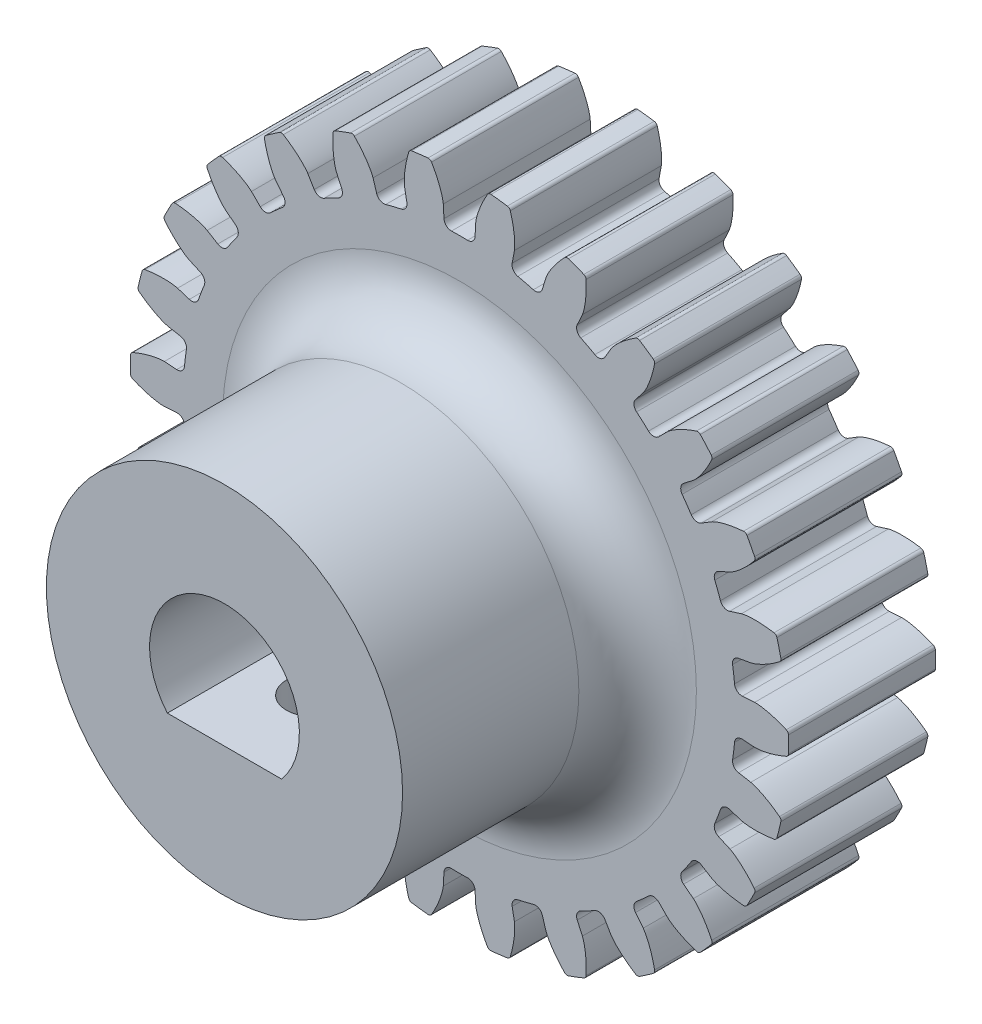
SolidWorks part; units mm, degrees
material "ABS"
ref_plane "Front" through (0, 0, 0) normal (0, 0, 1) x (1, 0, 0)
ref_plane "Top" through (0, 0, 0) normal (0, 1, 0) x (1, 0, 0)
ref_plane "Right" through (0, 0, 0) normal (1, 0, 0) x (0, 0, -1)
sketch "Sketch1" plane through (0, 0, 0) normal (0, 0, 1) x (1, 0, 0)
  circle A0 centre (0, 0) radius 14.224
extrude "Boss-Extrude1" add sketch "Sketch1" along normal blind 6.35
sketch "Sketch3" plane through (0, 0, 0) normal (0, 0, 1) x (1, 0, 0)
  line L0 (0, 0) -> (43.7181, 0) construction
  line L2 (0, 0) -> (-0.6547, 11.92) construction
  line L3 (0, 0) -> (0.6547, 11.92) construction
  line L4 (0.6547, 11.92) -> (0.7013, 12.768) construction
  line L5 (0, 0) -> (0, 61.276) construction
  line L6 (-0.6547, 11.92) -> (-0.7013, 12.768) construction
  circle A0 centre (0, 0) radius 14.224 construction
  circle A1 centre (0, 0) radius 13.208 construction
  circle A2 centre (0, 0) radius 12.7873 construction
  arc A3 (0.6547, 11.92) -> (-0.6547, 11.92) centre (0, 0) ccw construction
  arc A5 (1.2601, 14.1681) -> (-1.2601, 14.1681) centre (0, 0) ccw
  spline S0 degree 4 poles (-0.7013, 12.768) (-0.7014, 12.7703) (-0.7019, 12.7766) (-0.7031, 12.7884) (-0.7055, 12.8077) (-0.709, 12.8323) (-0.7143, 12.864) (-0.7215, 12.9013) (-0.7302, 12.9422) (-0.7407, 12.9866) (-0.752, 13.0308) (-0.7641, 13.0749) (-0.777, 13.1187) (-0.7933, 13.1717) (-0.8142, 13.2351) (-0.8403, 13.3091) (-0.872, 13.3928) (-0.9064, 13.4778) (-0.9422, 13.5612) (-0.9804, 13.6452) (-1.0189, 13.7264) (-1.061, 13.8104) (-1.1009, 13.8878) (-1.148, 13.9742) (-1.1867, 14.0438) (-1.2403, 14.1353) (-1.2727, 14.1892) (-1.3115, 14.2522) (-1.3292, 14.2801) (-1.3401, 14.2973) knots 0 0 0 0 0 0.005377 0.015084 0.028532 0.04661 0.064855 0.092111 0.119476 0.146842 0.174209 0.201575 0.228941 0.256307 0.307035 0.361767 0.4165 0.471232 0.525964 0.580697 0.635429 0.690161 0.744894 0.799626 0.854358 0.909091 0.954545 1 1 1 1 1 construction
  spline S1 degree 4 poles (-0.7013, 12.768) (-0.7014, 12.7703) (-0.7019, 12.7766) (-0.7031, 12.7884) (-0.7055, 12.8077) (-0.709, 12.8323) (-0.7143, 12.864) (-0.7215, 12.9013) (-0.7302, 12.9422) (-0.7407, 12.9866) (-0.752, 13.0308) (-0.7641, 13.0749) (-0.777, 13.1187) (-0.7933, 13.1717) (-0.8142, 13.2351) (-0.8403, 13.3091) (-0.872, 13.3928) (-0.9064, 13.4778) (-0.9422, 13.5612) (-0.9804, 13.6452) (-1.0189, 13.7264) (-1.061, 13.8104) (-1.1009, 13.8878) (-1.148, 13.9742) (-1.1867, 14.0438) (-1.2287, 14.1154) (-1.2494, 14.1503) (-1.2601, 14.1681) knots 0 0 0 0 0 0.005377 0.015084 0.028532 0.04661 0.064855 0.092111 0.119476 0.146842 0.174209 0.201575 0.228941 0.256307 0.307035 0.361767 0.4165 0.471232 0.525964 0.580697 0.635429 0.690161 0.744894 0.799626 0.854358 0.909091 0.909091 0.909091 0.909091 0.909091
  spline S2 degree 4 poles (0.7013, 12.768) (0.7014, 12.7703) (0.7019, 12.7766) (0.7031, 12.7884) (0.7055, 12.8077) (0.709, 12.8323) (0.7143, 12.864) (0.7215, 12.9013) (0.7302, 12.9422) (0.7407, 12.9866) (0.752, 13.0308) (0.7641, 13.0749) (0.777, 13.1187) (0.7933, 13.1717) (0.8142, 13.2351) (0.8403, 13.3091) (0.872, 13.3928) (0.9064, 13.4778) (0.9422, 13.5612) (0.9804, 13.6452) (1.0189, 13.7264) (1.061, 13.8104) (1.1009, 13.8878) (1.148, 13.9742) (1.1867, 14.0438) (1.2403, 14.1353) (1.2727, 14.1892) (1.3115, 14.2522) (1.3292, 14.2801) (1.3401, 14.2973) knots 0 0 0 0 0 0.005377 0.015084 0.028532 0.04661 0.064855 0.092111 0.119476 0.146842 0.174209 0.201575 0.228941 0.256307 0.307035 0.361767 0.4165 0.471232 0.525964 0.580697 0.635429 0.690161 0.744894 0.799626 0.854358 0.909091 0.954545 1 1 1 1 1 construction
  spline S3 degree 4 poles (0.7013, 12.768) (0.7014, 12.7703) (0.7019, 12.7766) (0.7031, 12.7884) (0.7055, 12.8077) (0.709, 12.8323) (0.7143, 12.864) (0.7215, 12.9013) (0.7302, 12.9422) (0.7407, 12.9866) (0.752, 13.0308) (0.7641, 13.0749) (0.777, 13.1187) (0.7933, 13.1717) (0.8142, 13.2351) (0.8403, 13.3091) (0.872, 13.3928) (0.9064, 13.4778) (0.9422, 13.5612) (0.9804, 13.6452) (1.0189, 13.7264) (1.061, 13.8104) (1.1009, 13.8878) (1.148, 13.9742) (1.1867, 14.0438) (1.2287, 14.1154) (1.2494, 14.1503) (1.2601, 14.1681) knots 0 0 0 0 0 0.005377 0.015084 0.028532 0.04661 0.064855 0.092111 0.119476 0.146842 0.174209 0.201575 0.228941 0.256307 0.307035 0.361767 0.4165 0.471232 0.525964 0.580697 0.635429 0.690161 0.744894 0.799626 0.854358 0.909091 0.909091 0.909091 0.909091 0.909091
  point P0 (0, 11.938)
sketch "DCLTBC" plane through (0, 0, 0) normal (0, 0, 1) x (1, 0, 0)
  line L0 (0, 0) -> (41.04, 0) construction
  line L1 (-0.6547, 11.92) -> (-0.7013, 12.768) construction
  line L2 (0.6547, 11.92) -> (0.7013, 12.768) construction
  line L3 (-0.6547, 11.92) -> (-0.7013, 12.768)
  line L4 (0.6547, 11.92) -> (0.7013, 12.768)
  line L5 (0, 0) -> (0, 104.9356) construction
  circle A0 centre (0, 0) radius 14.224
  circle A1 centre (0, 0) radius 13.208 construction
  circle A2 centre (0, 0) radius 12.7873 construction
  arc A3 (0.6547, 11.92) -> (-0.6547, 11.92) centre (0, 0) ccw construction
  arc A4 (0.6547, 11.92) -> (-0.6547, 11.92) centre (0, 0) ccw
  spline S0 degree 4 poles (-997.5218, -66.5121) (-10.52, 11.3394) (-0.7979, 12.1584) (-0.6668, 12.4893) (-0.7055, 12.8077) (-0.709, 12.8323) (-0.7143, 12.864) (-0.7215, 12.9013) (-0.7302, 12.9422) (-0.7407, 12.9866) (-0.752, 13.0308) (-0.7641, 13.0749) (-0.777, 13.1187) (-0.7933, 13.1717) (-0.8142, 13.2351) (-0.8403, 13.3091) (-0.872, 13.3928) (-0.9064, 13.4778) (-0.9422, 13.5612) (-0.9804, 13.6452) (-1.0189, 13.7264) (-1.061, 13.8104) (-1.1009, 13.8878) (-1.148, 13.9742) (-1.3672, 14.3683) (-2.2498, 15.7567) (10.602, -5.7239) (-517.3013, 870.6887) knots -0.722064 -0.722064 -0.722064 -0.722064 -0.722064 0.005377 0.015084 0.028532 0.04661 0.064855 0.092111 0.119476 0.146842 0.174209 0.201575 0.228941 0.256307 0.307035 0.361767 0.4165 0.471232 0.525964 0.580697 0.635429 0.690161 0.744894 0.799626 0.854358 1.929512 1.929512 1.929512 1.929512 1.929512 only from (-0.7013, 12.768) to (-1.2601, 14.1681) construction
  spline S1 degree 4 poles (997.5218, -66.5121) (10.52, 11.3394) (0.7979, 12.1584) (0.6668, 12.4893) (0.7055, 12.8077) (0.709, 12.8323) (0.7143, 12.864) (0.7215, 12.9013) (0.7302, 12.9422) (0.7407, 12.9866) (0.752, 13.0308) (0.7641, 13.0749) (0.777, 13.1187) (0.7933, 13.1717) (0.8142, 13.2351) (0.8403, 13.3091) (0.872, 13.3928) (0.9064, 13.4778) (0.9422, 13.5612) (0.9804, 13.6452) (1.0189, 13.7264) (1.061, 13.8104) (1.1009, 13.8878) (1.148, 13.9742) (1.3672, 14.3683) (2.2498, 15.7567) (-10.602, -5.7239) (517.3013, 870.6887) knots -0.722064 -0.722064 -0.722064 -0.722064 -0.722064 0.005377 0.015084 0.028532 0.04661 0.064855 0.092111 0.119476 0.146842 0.174209 0.201575 0.228941 0.256307 0.307035 0.361767 0.4165 0.471232 0.525964 0.580697 0.635429 0.690161 0.744894 0.799626 0.854358 1.929512 1.929512 1.929512 1.929512 1.929512 only from (0.7013, 12.768) to (1.2601, 14.1681) construction
  spline S2 degree 4 poles (-0.7013, 12.768) (-0.7014, 12.7703) (-0.7019, 12.7766) (-0.7031, 12.7884) (-0.7055, 12.8077) (-0.709, 12.8323) (-0.7143, 12.864) (-0.7215, 12.9013) (-0.7302, 12.9422) (-0.7407, 12.9866) (-0.752, 13.0308) (-0.7641, 13.0749) (-0.777, 13.1187) (-0.7933, 13.1717) (-0.8142, 13.2351) (-0.8403, 13.3091) (-0.872, 13.3928) (-0.9064, 13.4778) (-0.9422, 13.5612) (-0.9804, 13.6452) (-1.0189, 13.7264) (-1.061, 13.8104) (-1.1009, 13.8878) (-1.148, 13.9742) (-1.1867, 14.0438) (-1.2287, 14.1154) (-1.2494, 14.1503) (-1.2601, 14.1681) knots 0 0 0 0 0 0.005377 0.015084 0.028532 0.04661 0.064855 0.092111 0.119476 0.146842 0.174209 0.201575 0.228941 0.256307 0.307035 0.361767 0.4165 0.471232 0.525964 0.580697 0.635429 0.690161 0.744894 0.799626 0.854358 0.909091 0.909091 0.909091 0.909091 0.909091
  spline S3 degree 4 poles (0.7013, 12.768) (0.7014, 12.7703) (0.7019, 12.7766) (0.7031, 12.7884) (0.7055, 12.8077) (0.709, 12.8323) (0.7143, 12.864) (0.7215, 12.9013) (0.7302, 12.9422) (0.7407, 12.9866) (0.752, 13.0308) (0.7641, 13.0749) (0.777, 13.1187) (0.7933, 13.1717) (0.8142, 13.2351) (0.8403, 13.3091) (0.872, 13.3928) (0.9064, 13.4778) (0.9422, 13.5612) (0.9804, 13.6452) (1.0189, 13.7264) (1.061, 13.8104) (1.1009, 13.8878) (1.148, 13.9742) (1.1867, 14.0438) (1.2287, 14.1154) (1.2494, 14.1503) (1.2601, 14.1681) knots 0 0 0 0 0 0.005377 0.015084 0.028532 0.04661 0.064855 0.092111 0.119476 0.146842 0.174209 0.201575 0.228941 0.256307 0.307035 0.361767 0.4165 0.471232 0.525964 0.580697 0.635429 0.690161 0.744894 0.799626 0.854358 0.909091 0.909091 0.909091 0.909091 0.909091
extrude "Cut-Extrude-DCLTBC" cut sketch "DCLTBC" along normal through all
fillet "Fillet-Tip-DCLTBC" radius 0.1588 2 edges at (1.2601, 14.1681, 3.175) (-1.2601, 14.1681, 3.175)
fillet "Fillet-Root-DCLTBC" radius 0.3176 2 edges at (-0.6547, 11.92, 3.175) (0.6547, 11.92, 3.175)
pattern_circular "CirPattern-DCLTBC" count 26 over 360 about axis through (0, 0, 6.35) along (0, 0, 1) of "Cut-Extrude-DCLTBC", "Fillet-Tip-DCLTBC", "Fillet-Root-DCLTBC"
sketch "DCGTBC" [suppressed] plane through (0, 0, 0) normal (0, 0, 1) x (1, 0, 0)
  line L0 (0, 0) -> (41.04, 0) construction
  line L1 (-37.3224, 3.2653) -> (0, 0) construction
  line L2 (0, 0) -> (37.3224, 3.2653) construction
  line L3 (0, 0) -> (-16.5124, 0)
  line L5 (0, 0) -> (0, 104.9356) construction
  circle A0 centre (0, 0) radius 38.608
  circle A1 centre (0, 0) radius 38.1 construction
  circle A2 centre (0, 0) radius 36.8864 construction
  arc A3 (0.1846, 37.4645) -> (-0.1846, 37.4645) centre (0, 0) ccw construction
  arc A11 (37.3224, 3.2653) -> (-37.3224, 3.2653) centre (0, 0) ccw
  spline S4 degree 4 poles (999.1092, -9.1639) (9.2917, 35.7604) (0.2917, 36.1338) (0.1647, 36.5321) (0.1834, 36.9323) (0.1852, 36.961) (0.188, 36.9982) (0.192, 37.0421) (0.197, 37.0904) (0.2032, 37.143) (0.21, 37.1956) (0.2175, 37.2482) (0.2254, 37.3006) (0.2357, 37.3641) (0.2489, 37.4405) (0.2657, 37.53) (0.2863, 37.6318) (0.309, 37.7359) (0.3327, 37.8385) (0.3583, 37.9426) (0.3842, 38.0436) (0.4127, 38.1489) (0.4399, 38.2463) (0.4722, 38.3558) (0.6183, 38.8417) (1.2009, 40.5477) (-6.8048, 15.7351) (309.5446, 989.6637) knots -0.780323 -0.780323 -0.780323 -0.780323 -0.780323 0.005377 0.015084 0.028532 0.04661 0.064855 0.092111 0.119476 0.146842 0.174209 0.201575 0.228941 0.256307 0.307035 0.361767 0.4165 0.471232 0.525964 0.580697 0.635429 0.690161 0.744894 0.799626 0.854358 1.89102 1.89102 1.89102 1.89102 1.89102 only from (0.1817, 36.886) to (0.5498, 38.6041) construction
  spline S5 degree 4 poles (-999.1092, -9.1639) (-9.2917, 35.7604) (-0.2917, 36.1338) (-0.1647, 36.5321) (-0.1834, 36.9323) (-0.1852, 36.961) (-0.188, 36.9982) (-0.192, 37.0421) (-0.197, 37.0904) (-0.2032, 37.143) (-0.21, 37.1956) (-0.2175, 37.2482) (-0.2254, 37.3006) (-0.2357, 37.3641) (-0.2489, 37.4405) (-0.2657, 37.53) (-0.2863, 37.6318) (-0.309, 37.7359) (-0.3327, 37.8385) (-0.3583, 37.9426) (-0.3842, 38.0436) (-0.4127, 38.1489) (-0.4399, 38.2463) (-0.4722, 38.3558) (-0.6183, 38.8417) (-1.2009, 40.5477) (6.8048, 15.7351) (-309.5446, 989.6637) knots -0.780323 -0.780323 -0.780323 -0.780323 -0.780323 0.005377 0.015084 0.028532 0.04661 0.064855 0.092111 0.119476 0.146842 0.174209 0.201575 0.228941 0.256307 0.307035 0.361767 0.4165 0.471232 0.525964 0.580697 0.635429 0.690161 0.744894 0.799626 0.854358 1.89102 1.89102 1.89102 1.89102 1.89102 only from (-0.1817, 36.886) to (-0.5498, 38.6041) construction
  spline S6 degree 4 poles (0.1817, 36.886) (0.1818, 36.8886) (0.1819, 36.8959) (0.1824, 36.9097) (0.1834, 36.9323) (0.1852, 36.961) (0.188, 36.9982) (0.192, 37.0421) (0.197, 37.0904) (0.2032, 37.143) (0.21, 37.1956) (0.2175, 37.2482) (0.2254, 37.3006) (0.2357, 37.3641) (0.2489, 37.4405) (0.2657, 37.53) (0.2863, 37.6318) (0.309, 37.7359) (0.3327, 37.8385) (0.3583, 37.9426) (0.3842, 38.0436) (0.4127, 38.1489) (0.4399, 38.2463) (0.4722, 38.3558) (0.4989, 38.4444) (0.5279, 38.5364) (0.5423, 38.5812) (0.5498, 38.6041) knots 0 0 0 0 0 0.005377 0.015084 0.028532 0.04661 0.064855 0.092111 0.119476 0.146842 0.174209 0.201575 0.228941 0.256307 0.307035 0.361767 0.4165 0.471232 0.525964 0.580697 0.635429 0.690161 0.744894 0.799626 0.854358 0.909091 0.909091 0.909091 0.909091 0.909091
  spline S7 degree 4 poles (-0.1817, 36.886) (-0.1818, 36.8886) (-0.1819, 36.8959) (-0.1824, 36.9097) (-0.1834, 36.9323) (-0.1852, 36.961) (-0.188, 36.9982) (-0.192, 37.0421) (-0.197, 37.0904) (-0.2032, 37.143) (-0.21, 37.1956) (-0.2175, 37.2482) (-0.2254, 37.3006) (-0.2357, 37.3641) (-0.2489, 37.4405) (-0.2657, 37.53) (-0.2863, 37.6318) (-0.309, 37.7359) (-0.3327, 37.8385) (-0.3583, 37.9426) (-0.3842, 38.0436) (-0.4127, 38.1489) (-0.4399, 38.2463) (-0.4722, 38.3558) (-0.4989, 38.4444) (-0.5279, 38.5364) (-0.5423, 38.5812) (-0.5498, 38.6041) knots 0 0 0 0 0 0.005377 0.015084 0.028532 0.04661 0.064855 0.092111 0.119476 0.146842 0.174209 0.201575 0.228941 0.256307 0.307035 0.361767 0.4165 0.471232 0.525964 0.580697 0.635429 0.690161 0.744894 0.799626 0.854358 0.909091 0.909091 0.909091 0.909091 0.909091
  dimension "D1" = 5
  dimension "D2" = 5
extrude "Cut-Extrude-DCGTBC" [suppressed] cut sketch "DCGTBC" along normal through all
fillet "Fillet-Tip-DCGTBC" [suppressed] radius 0.1588
pattern_circular "CirPattern-DCGTBC" [suppressed] count 26 over 360
sketch "Sketch4" plane through (0, 0, 6.35) normal (0, 0, 1) x (1, 0, 0)
  line L0 (-2.4692, -2.0955) -> (2.4692, -2.0955)
  arc A0 (2.4692, -2.0955) -> (-2.4692, -2.0955) centre (0, 0) ccw
  circle A1 centre (0, 0) radius 5.1594
  point P3 (0, 3.2385)
  dimension "D1" = 6.477
  dimension "D3" = 10.3187
  dimension "D2" = 5.334
extrude "Cut-Extrude2" cut sketch "Sketch4" against normal through all contours L0 A0 | A1 A0 L0
sketch "Sketch5" plane through (0, 0, 6.35) normal (0, 0, 1) x (1, 0, 0)
  line L0 (-2.4692, -2.0955) -> (2.4692, -2.0955) construction
  line L1 (-2.4692, -2.0955) -> (2.4692, -2.0955)
  circle A0 centre (0, 0) radius 7.6994
  circle A1 centre (0, 0) radius 5.1594 construction
  arc A2 (2.4692, -2.0955) -> (-2.4692, -2.0955) centre (0, 0) ccw construction
  arc A3 (2.4692, -2.0955) -> (-2.4692, -2.0955) centre (0, 0) ccw
  dimension "D1" = 2.54
extrude "Boss-Extrude2" add sketch "Sketch5" along normal blind 10.16
fillet "Fillet1" radius 2.54 1 edges at (7.6994, 0, 6.35)
ref_plane "Plane1" through (0, -7.6994, 16.51) normal (0, -1, 0) x (-1, 0, 0)
hole_wizard "#4-40 Tapped Hole1" positions "Sketch8" profile "Sketch7" tap size "#4-40" standard "ANSI Inch"
sketch "Sketch8" plane through (0, -7.6994, 16.51) normal (0, -1, 0) x (-1, 0, 0)
  line L0 (0, 0) -> (0, 7.62) construction
  line L2 (-7.6994, 7.62) -> (7.6994, 7.62) construction
  line L3 (-7.6994, 0) -> (7.6994, 0) construction
  point P12 (0, 3.81)
sketch "Sketch7" plane through (0, -7.6994, 12.7) normal (1, 0, 0) x (0, 0, -1)
  line L0 (0, 0) -> (0, 5.6039)
  line L1 (0, 5.6039) -> (1.1303, 5.6039)
  line L2 (1.1303, 5.6039) -> (1.1303, 0.5328)
  line L3 (1.1303, 0.5328) -> (1.7653, 0)
  line L5 (1.7653, 0) -> (0, 0)
  line L6 (-1.1303, 0.5328) -> (-1.7653, 0) construction
  line L11 (0, -6.35) -> (0, 107.95) construction
  dimension "Thru Tap Drill Dia." = 2.2606
  dimension "Thru Tap Drill Depth" = 5.6039
  dimension "Near C'Sink Dia." = 3.5306
  dimension "Near C'Sink Angle" = 100
cosmetic thread "Hole Thread1" parameters "D2"=2.8448
equation "\"DiametralPitch\"= 25'Diametral Pitch"
equation "\"NumTeeth\"= 26'Number of Teeth"
equation "\"PressureAngle\"= 14.5deg'Pressure Angle"
equation "\"Addendum\"= 1 / \"DiametralPitch\"'Addendum"
equation "\"Dedendum\"= 1.25 / \"DiametralPitch\"'Dedendum"
equation "\"WorkingDepth\"= 2 / \"DiametralPitch\"'Working Depth - here for REF (Not used in building model)"
equation "\"WholeDepth\"= 2.25 / \"DiametralPitch\"'Whole Depth - here for REF (Not used in building model)"
equation "\"Clearance\"= .25 / \"DiametralPitch\"'Clearance"
equation "\"CircularPitch\"= pi / \"DiametralPitch\"'Circular Pitch - here for REF (Not used in building model)"
equation "\"PitchCircle\"= \"NumTeeth\" / \"DiametralPitch\"'Pitch Circle - or - Pitch Diameter"
equation "\"OutsideDiameter\"= ( \"NumTeeth\" + 2 ) / \"DiametralPitch\"'Outside Diameter"
equation "\"Fillet_Root\"= \"Clearance\" * cos ( \"PressureAngle\" ) * tan ( ( 90 + \"PressureAngle\" ) / 2 ) 'Fillet Root"
equation "\"AddendumCircle\"= \"PitchCircle\" + ( 2 * \"Addendum\" )'Addendum Circle - or - Addendum Diameter"
equation "\"DedendumCircle\"= \"PitchCircle\" - ( 2 * \"Dedendum\" )'Dedendum Circle - or - Dedendum Diameter"
equation "\"BaseCircle\"= \"PitchCircle\" * cos ( \"PressureAngle\" )'Base Circle - Base Diameter"
equation "\"PitchAngle\"= 360deg / \"NumTeeth\"'Pitch Angle"
equation "\"Alpha\"= sqr ( \"PitchCircle\" ^ 2 - \"BaseCircle\" ^ 2 ) / \"BaseCircle\" * 180 / PI - \"PressureAngle\"'Alpha - Used for Calculating Beta"
equation "\"Beta\"= ( \"PitchAngle\" / 4 - ( \"Alpha\" - 90 ) )'Beta - Used in definition of the parameters for the parametric equation driven curve"
equation "\"Gamma\"= ( \"PitchAngle\" / 4 - ( \"Alpha\" + 90 ) )'Gamma - Used in definition of the parameters for the parametric equation driven curve"
equation "\"Phi\"= sqr ( ( \"AddendumCircle\" / 2 ) ^ 2 - ( \"BaseCircle\" / 2 ) ^ 2 ) / ( \"BaseCircle\" / 2 )'Phi - Used in definition of the parameters for the parametric equation driven curve"
equation "\"DCGTBC\"= iif ( \"DedendumCircle\" > \"BaseCircle\" , \"unsuppressed\" , \"suppressed\" )'if Dedendum Circle IS GREATER THAN BaseCircle THEN UnsuppressORSuppress FEATURE"
equation "\"DCLTBC\"= iif ( \"DedendumCircle\" - .002 > \"BaseCircle\" , \"suppressed\" , \"unsuppressed\" )'if Dedendum Circle - .002 IS GREATER THAN BaseCircle THEN SuppressORUnsuppress FEATURE"
equation "\"Cut-Extrude-DCGTBC\"= iif ( \"DedendumCircle\" > \"BaseCircle\" , \"unsuppressed\" , \"suppressed\" )'if Dedendum Circle IS GREATER THAN BaseCircle THEN UnsuppressORSuppress FEATURE"
equation "\"Cut-Extrude-DCLTBC\"= iif ( \"DedendumCircle\" - .002 > \"BaseCircle\" , \"suppressed\" , \"unsuppressed\" )'if Dedendum Circle - .002 IS GREATER THAN BaseCircle THEN SuppressORUnsuppress FEATURE"
equation "\"CirPattern-DCGTBC\"= iif ( \"DedendumCircle\" > \"BaseCircle\" , \"unsuppressed\" , \"suppressed\" )'if Dedendum Circle IS GREATER THAN BaseCircle THEN UnsuppressORSuppress FEATURE"
equation "\"CirPattern-DCLTBC\"= iif ( \"DedendumCircle\" - .002 > \"BaseCircle\" , \"suppressed\" , \"unsuppressed\" )'if Dedendum Circle - .002 IS GREATER THAN BaseCircle THEN SuppressORUnsuppress FEATURE"
equation "\"Fillet-Tip-DCGTBC\"= iif ( \"DedendumCircle\" > \"BaseCircle\" , \"unsuppressed\" , \"suppressed\" )'if Dedendum Circle IS GREATER THAN BaseCircle THEN UnsuppressORSuppress FEATURE"
equation "\"Fillet-Tip-DCLTBC\"= iif ( \"DedendumCircle\" - .002 > \"BaseCircle\" , \"suppressed\" , \"unsuppressed\" )'if Dedendum Circle - .002 IS GREATER THAN BaseCircle THEN SuppressORUnsuppress FEATURE"
equation "\"Fillet-Root-DCLTBC\"= iif ( \"DedendumCircle\" - .002 > \"BaseCircle\" , \"suppressed\" , \"unsuppressed\" )'if Dedendum Circle - .002 IS GREATER THAN BaseCircle THEN SuppressORUnsuppress FEATURE"
equation "\"D1@CirPattern-DCGTBC\"= \"NumTeeth\"'Number of Teeth"
equation "\"D1@CirPattern-DCLTBC\"= \"NumTeeth\"'Number of Teeth"
equation "\"D1@Fillet-Tip-DCGTBC\"= \"Fillet_Root\" / 2 'Tip Rad For Large No of Teeth"
equation "\"D1@Fillet-Tip-DCLTBC\"=\"Fillet_Root\" / 2'Tip Rad For Small No of Teeth"
equation "\"D1@Fillet-Root-DCLTBC\"= \"Fillet_Root\"'Fillet Root"
